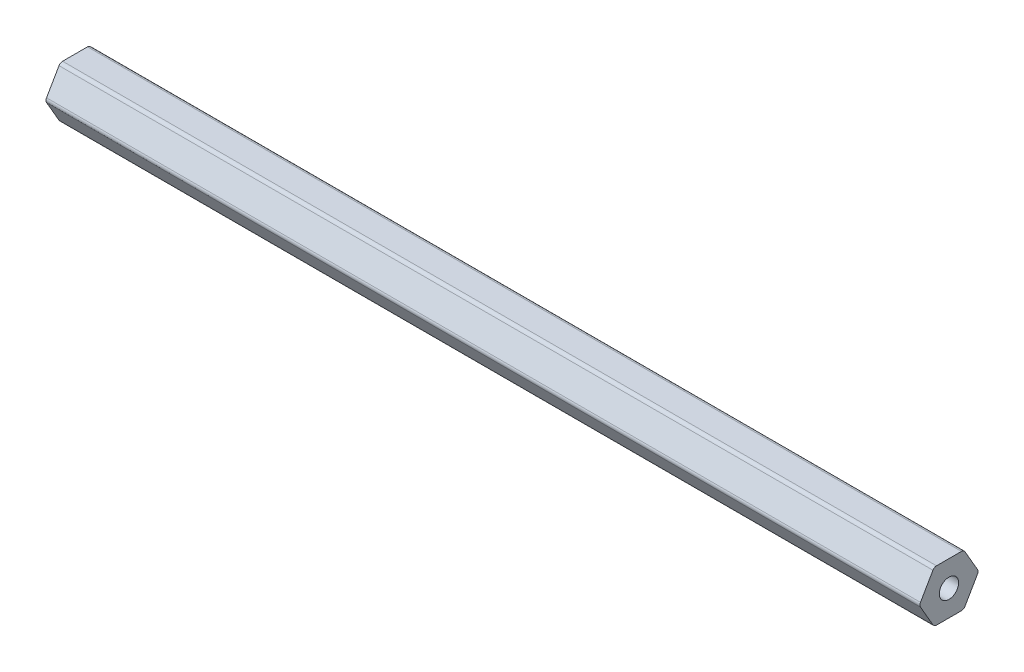
SolidWorks part; units mm, degrees
material "7075-T6 (SN)"
ref_plane "Front Plane" through (0, 0, 0) normal (0, 0, 1) x (1, 0, 0)
ref_plane "Top Plane" through (0, 0, 0) normal (0, 1, 0) x (1, 0, 0)
ref_plane "Right Plane" through (0, 0, 0) normal (1, 0, 0) x (0, 0, -1)
sketch "Sketch1" plane through (0, 0, 0) normal (1, 0, 0) x (0, 0, -1)
  line L1 (7.0391, 0.508) -> (3.9595, 5.842)
  line L2 (3.0796, 6.35) -> (-3.0796, 6.35)
  line L3 (-3.9595, 5.842) -> (-7.0391, 0.508)
  line L4 (-7.0391, -0.508) -> (-3.9595, -5.842)
  line L5 (-3.0796, -6.35) -> (3.0796, -6.35)
  line L6 (3.9595, -5.842) -> (7.0391, -0.508)
  circle A0 centre (0, 0) radius 6.35 construction
  arc A1 (3.0796, 6.35) -> (3.9595, 5.842) centre (3.0796, 5.334) cw
  arc A2 (7.0391, 0.508) -> (7.0391, -0.508) centre (6.1592, 0) cw
  arc A3 (3.9595, -5.842) -> (3.0796, -6.35) centre (3.0796, -5.334) cw
  arc A4 (-3.0796, -6.35) -> (-3.9595, -5.842) centre (-3.0796, -5.334) cw
  arc A5 (-7.0391, -0.508) -> (-7.0391, 0.508) centre (-6.1592, 0) cw
  arc A6 (-3.9595, 5.842) -> (-3.0796, 6.35) centre (-3.0796, 5.334) cw
  circle A7 centre (0, 0) radius 2.3813
  point P11 (3.6662, 6.35)
  point P14 (7.3323, 0)
  dimension "D1" = 12.7
  dimension "D3" = 1.016
  dimension "D4" = 4.7625
  dimension "D2" = 6.35
extrude "Boss-Extrude1" add sketch "Sketch1" along normal blind 215.9
